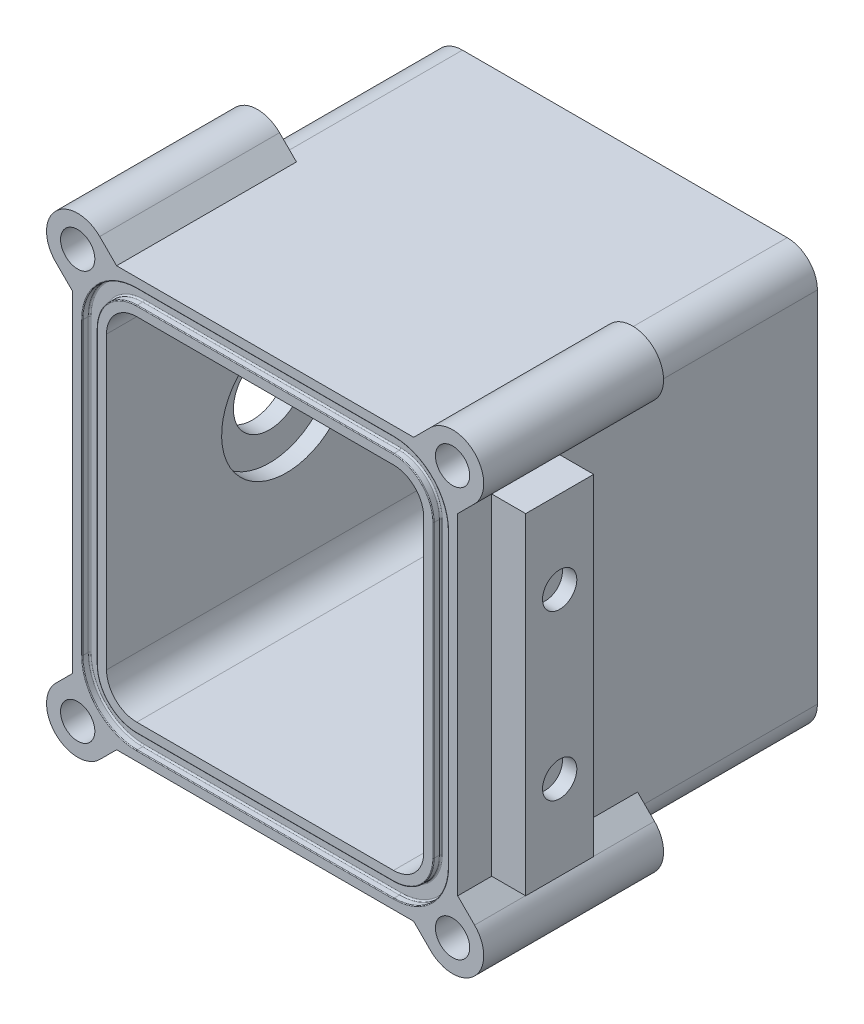
SolidWorks part; units mm, degrees
material "ABS"
ref_plane "X-Y Datum" through (0, 0, 0) normal (0, 0, 1) x (1, 0, 0)
ref_plane "X-Z Datum" through (0, 0, 0) normal (0, 1, 0) x (1, 0, 0)
ref_plane "Y-Z Datum" through (0, 0, 0) normal (1, 0, 0) x (0, 0, -1)
sketch "Sketch1" plane through (0, 0, 0) normal (0, 0, 1) x (1, 0, 0)
  line L0 (-34, -37) -> (-34, -16.68)
  line L1 (34, 37) -> (-34, 37)
  line L2 (34, 37) -> (34, -37)
  line L3 (34, -37) -> (-34, -37)
  line L5 (34, 37) -> (-34, -37) construction
  line L6 (34, -37) -> (-34, 37) construction
  line L7 (55.1739, 0) -> (-55.1739, 0) construction
  line L8 (-34, 37) -> (-34, 16.68)
  line L9 (-34, 16.68) -> (-34, -16.68)
  arc A0 (-34, -16.68) -> (-34, 16.68) centre (-14.8444, 0) cw construction
  point P0 (0, 0)
  dimension "D2" = 25.4
  dimension "D1" = 74
  dimension "D3" = 20.32
  dimension "D4" = 68
extrude "Boss-Extrude1" add sketch "Sketch1" along normal mid plane 63.5
shell "Shell1" thickness 6
fillet "Fillet1" radius 5.334 8 edges at (34, 37, 0) (34, -37, 0) (-34, -37, 0) (-34, 37, 0) (28, 31, 3) (28, -31, 3) (-28, -31, 3) (-28, 31, 3)
sketch "Sketch2" plane through (0, 0, 31.75) normal (0, 0, 1) x (1, 0, 0)
  line L21 (32.2827, -25.666) -> (32.2827, 25.666)
  line L22 (22.666, 35.2827) -> (-22.666, 35.2827)
  line L23 (-32.2827, 25.666) -> (-32.2827, -25.666)
  line L24 (-22.666, -35.2827) -> (22.666, -35.2827)
  line L25 (31, -25.666) -> (31, 25.666)
  line L26 (-22.666, -34) -> (22.666, -34)
  line L27 (-31, 25.666) -> (-31, -25.666)
  line L28 (22.666, 34) -> (-22.666, 34)
  line L29 (31, -25.666) -> (31, 25.666) construction
  line L30 (-22.666, -34) -> (22.666, -34) construction
  line L31 (-31, 25.666) -> (-31, -25.666) construction
  line L32 (22.666, 34) -> (-22.666, 34) construction
  line L33 (-29.7173, 25.666) -> (-29.7173, -25.666)
  line L34 (-22.666, -32.7173) -> (22.666, -32.7173)
  line L35 (29.7173, -25.666) -> (29.7173, 25.666)
  line L36 (22.666, 32.7173) -> (-22.666, 32.7173)
  arc A15 (32.2827, 25.666) -> (22.666, 35.2827) centre (22.666, 25.666) ccw
  arc A16 (-22.666, 35.2827) -> (-32.2827, 25.666) centre (-22.666, 25.666) ccw
  arc A17 (-32.2827, -25.666) -> (-22.666, -35.2827) centre (-22.666, -25.666) ccw
  arc A18 (22.666, -35.2827) -> (32.2827, -25.666) centre (22.666, -25.666) ccw
  arc A19 (31, 25.666) -> (22.666, 34) centre (22.666, 25.666) ccw
  arc A20 (22.666, -34) -> (31, -25.666) centre (22.666, -25.666) ccw
  arc A21 (-31, -25.666) -> (-22.666, -34) centre (-22.666, -25.666) ccw
  arc A22 (-22.666, 34) -> (-31, 25.666) centre (-22.666, 25.666) ccw
  arc A23 (31, 25.666) -> (22.666, 34) centre (22.666, 25.666) ccw construction
  arc A24 (22.666, -34) -> (31, -25.666) centre (22.666, -25.666) ccw construction
  arc A25 (-31, -25.666) -> (-22.666, -34) centre (-22.666, -25.666) ccw construction
  arc A26 (-22.666, 34) -> (-31, 25.666) centre (-22.666, 25.666) ccw construction
  arc A27 (-22.666, 32.7173) -> (-29.7173, 25.666) centre (-22.666, 25.666) ccw
  arc A28 (-29.7173, -25.666) -> (-22.666, -32.7173) centre (-22.666, -25.666) ccw
  arc A29 (22.666, -32.7173) -> (29.7173, -25.666) centre (22.666, -25.666) ccw
  arc A30 (29.7173, 25.666) -> (22.666, 32.7173) centre (22.666, 25.666) ccw
  dimension "D4" = 7.0513
  dimension "D5" = 2.5654
  dimension "D1" = 3
  dimension "D2" = 1.2827
  dimension "D3" = 1.2827
extrude "Cut-Extrude1" cut sketch "Sketch2" against normal blind 1.2954
fillet "Fillet2" radius 0.254 16 edges at (27.652, -30.652, 30.4546) (0, -32.7173, 30.4546) (-27.652, -30.652, 30.4546) (-29.7173, 0, 30.4546) (-27.652, 30.652, 30.4546) (0, 32.7173, 30.4546) (27.652, 30.652, 30.4546) (-29.466, 32.466, 30.4546) (0, 35.2827, 30.4546) (29.466, 32.466, 30.4546) (32.2827, 0, 30.4546) (29.466, -32.466, 30.4546) (0, -35.2827, 30.4546) (-29.466, -32.466, 30.4546) (29.7173, 0, 30.4546) (-32.2827, 0, 30.4546)
fillet "Fillet3" radius 0.127 16 edges at (-29.466, -32.466, 31.75) (-32.2827, 0, 31.75) (-29.466, 32.466, 31.75) (0, 35.2827, 31.75) (29.466, 32.466, 31.75) (32.2827, 0, 31.75) (29.466, -32.466, 31.75) (-27.652, -30.652, 31.75) (-29.7173, 0, 31.75) (-27.652, 30.652, 31.75) (0, 32.7173, 31.75) (27.652, 30.652, 31.75) (29.7173, 0, 31.75) (27.652, -30.652, 31.75) (0, -35.2827, 31.75) (0, -32.7173, 31.75)
sketch "Sketch3" plane through (0, 0, 31.75) normal (0, 0, 1) x (1, 0, 0)
  line L0 (22.666, -25.666) -> (37.7124, -40.7124) construction
  line L1 (29.2023, -39.9805) -> (26.2218, -37)
  line L2 (-28.666, -37) -> (28.666, -37) construction
  line L3 (22.666, -25.666) -> (0, 0)
  line L5 (34, -29.2218) -> (36.9805, -32.2023)
  line L6 (34, -31.666) -> (34, 31.666) construction
  arc A0 (22.666, -35.4097) -> (32.4097, -25.666) centre (22.666, -25.666) ccw construction
  arc A1 (22.666, -35.4097) -> (32.4097, -25.666) centre (22.666, -25.666) ccw
  circle A2 centre (33.0914, -36.0914) radius 3.025
  circle A3 centre (33.0914, -36.0914) radius 5.5
  point P7 (29.5558, -32.5558)
  dimension "D1" = 6.05
  dimension "D3" = 11
  dimension "D2" = 5
extrude "Boss-Extrude2" add sketch "Sketch3" against normal blind 31.75
sketch "Sketch4" plane through (0, 0, 31.75) normal (0, 0, 1) x (1, 0, 0)
  circle A0 centre (33.0914, -36.0914) radius 3.025 construction
  circle A1 centre (33.0914, -36.0914) radius 3.025
  dimension "D1" = 6.05
extrude "Cut-Extrude2" cut sketch "Sketch4" against normal blind 9
mirror "Mirror1" about plane through (0, 0, 0) normal (0, 1, 0) of "Cut-Extrude2", "Boss-Extrude2"
mirror "Mirror2" about plane through (0, 0, 0) normal (1, 0, 0) of "Mirror1", "Cut-Extrude2", "Boss-Extrude2"
sketch "Sketch8" plane through (-34, 0, 0) normal (-1, 0, 0) x (0, 0, 1)
  line L0 (19.75, 29.2218) -> (19.75, -29.2218) construction
  line L11 (25.75, 29.2218) -> (25.75, -29.2218)
  line L12 (0, 29.2218) -> (31.75, 29.2218) construction
  line L13 (0, -29.2218) -> (31.75, -29.2218) construction
  line L14 (25.75, 29.2218) -> (13.75, 29.2218)
  line L15 (13.75, 29.2218) -> (13.75, -29.2218)
  line L16 (13.75, -29.2218) -> (25.75, -29.2218)
  line L17 (13.75, 0) -> (25.75, 0) construction
  line L18 (25.75, 29.2218) -> (13.75, 29.2218)
  line L19 (25.75, -29.2218) -> (13.75, -29.2218)
  point P0 (0, 0)
  line M1 (31.75, 29.2218) -> (0, 29.2218)
  line M7 (0, -29.2218) -> (31.75, -29.2218)
extrude "Boss-Extrude3" add sketch "Sketch8" along normal blind 6 contours L15 L11 M1 M7
sketch "Sketch12" plane through (-40, 0, 0) normal (-1, 0, 0) x (0, 0, 1)
  line L0 (19.75, 29.2218) -> (19.75, -29.2218) construction
  line L1 (25.75, 29.2218) -> (13.75, 29.2218) construction
  line L2 (13.75, -29.2218) -> (25.75, -29.2218) construction
  line L3 (13.75, 0) -> (25.75, 0) construction
  line L4 (13.75, 29.2218) -> (13.75, -29.2218) construction
  line L5 (25.75, 29.2218) -> (25.75, -29.2218) construction
  circle A0 centre (19.75, 14.6168) radius 3.025
  circle A1 centre (19.75, -14.3392) radius 3.025
  dimension "D1" = 14.605
  dimension "D3" = 6.05
  dimension "D2" = 6.05
extrude "Cut-Extrude6" cut sketch "Sketch12" against normal blind 2.54
sketch "Sketch13" plane through (-34, 0, 0) normal (-1, 0, 0) x (0, 0, 1)
  line L0 (-31.75, 0) -> (31.75, 0) construction
  line L3 (-31.75, 31.666) -> (-31.75, -31.666) construction
  line L4 (31.75, 29.2218) -> (31.75, -29.2218) construction
  circle A0 centre (0, 0) radius 6.35
  dimension "D2" = 12.7
extrude "Cut-Extrude10" cut sketch "Sketch13" against normal blind 6
sketch "Sketch16" plane through (-28, 0, 0) normal (1, 0, 0) x (0, 0, -1)
  circle A0 centre (0, 0) radius 11.43
  dimension "D1" = 22.86
extrude "Cut-Extrude14" cut sketch "Sketch16" against normal blind 3
mirror "Mirror5" about plane through (0, 0, 0) normal (1, 0, 0) of "Boss-Extrude3"
mirror "Mirror6" about plane through (0, 0, 0) normal (1, 0, 0) of "Cut-Extrude6"
